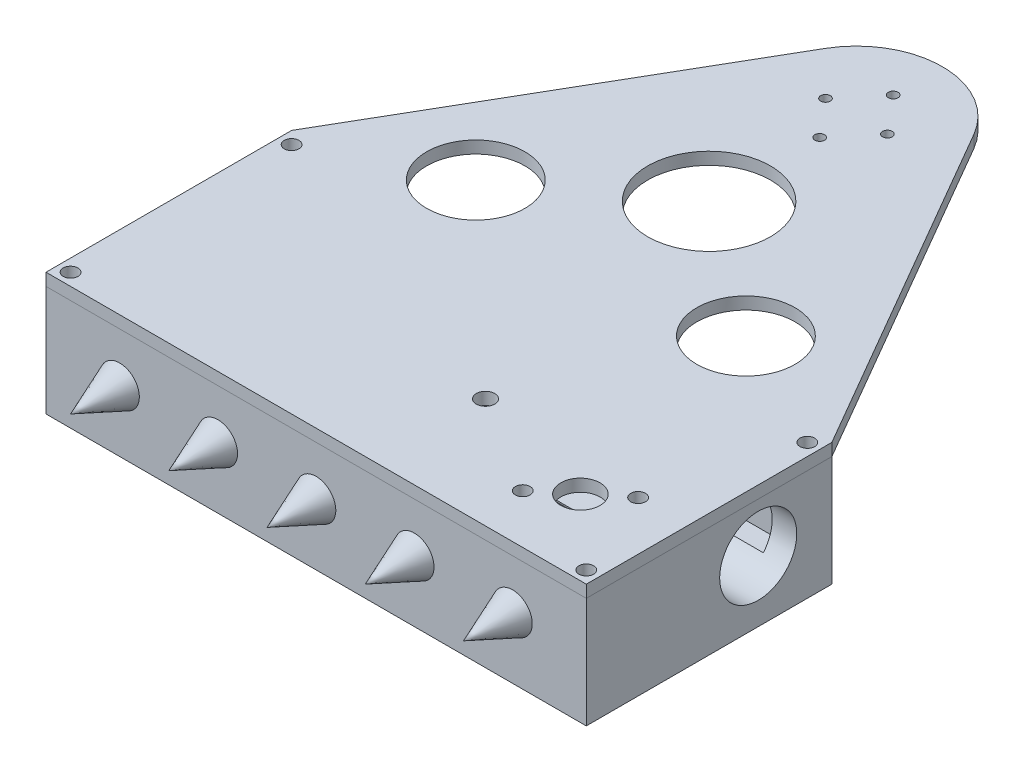
SolidWorks part; units mm, degrees
material "PLA/ABS"
ref_plane "Front Plane" through (0, 0, 0) normal (0, 0, 1) x (1, 0, 0)
ref_plane "Top Plane" through (0, 0, 0) normal (0, 1, 0) x (1, 0, 0)
ref_plane "Right Plane" through (0, 0, 0) normal (1, 0, 0) x (0, 0, -1)
other "Bounding Box"
ref_plane "Default Plane" through (-8.9266, -12.7485, 0) normal (-0.1736, 0.9848, 0) x (0.9848, 0.1736, 0)
sketch "Sketch1" plane through (0, 0, 0) normal (0, 1, 0) x (1, 0, 0)
  line L0 (0, 0) -> (0, -95.25) construction
  line L1 (0, -95.25) -> (-19.05, -95.25) construction
  line L2 (-76.2, -95.25) -> (-69.85, -95.25) construction
  line L3 (-69.85, -105.2195) -> (-19.05, -105.2195)
  line L4 (-69.85, -105.2195) -> (-69.85, -85.2805)
  line L5 (-69.85, -85.2805) -> (-19.05, -85.2805)
  line L6 (-19.05, -105.2195) -> (-19.05, -85.2805)
  line L7 (-69.85, -105.2195) -> (-19.05, -85.2805) construction
  line L8 (-69.85, -85.2805) -> (-19.05, -105.2195) construction
  line L9 (-88.9, -120.65) -> (-76.2, -120.65)
  line L10 (-88.9, -120.65) -> (-88.9, -69.85)
  line L11 (-88.9, -69.85) -> (-76.2, -69.85)
  line L12 (-76.2, -120.65) -> (-76.2, -69.85)
  line L13 (-88.9, -120.65) -> (-76.2, -69.85) construction
  line L14 (-88.9, -69.85) -> (-76.2, -120.65) construction
  line L15 (69.85, -85.2805) -> (19.05, -85.2805)
  line L16 (-63.5, -133.35) -> (-6.35, -133.35)
  line L17 (-63.5, -133.35) -> (-63.5, -116.84)
  line L18 (-63.5, -116.84) -> (-6.35, -116.84)
  line L19 (-6.35, -133.35) -> (-6.35, -116.84)
  line L20 (-63.5, -133.35) -> (-6.35, -116.84) construction
  line L21 (-63.5, -116.84) -> (-6.35, -133.35) construction
  line L22 (19.05, -105.2195) -> (19.05, -85.2805)
  line L23 (69.85, -105.2195) -> (19.05, -105.2195)
  line L24 (69.85, -105.2195) -> (69.85, -85.2805)
  line L25 (88.9, -69.85) -> (76.2, -69.85)
  line L26 (76.2, -120.65) -> (76.2, -69.85)
  line L27 (88.9, -120.65) -> (76.2, -120.65)
  line L28 (88.9, -120.65) -> (88.9, -69.85)
  line L30 (63.5, -133.35) -> (20.32, -133.35)
  line L31 (63.5, -133.35) -> (63.5, -113.2078)
  line L32 (63.5, -113.2078) -> (20.32, -113.2078)
  line L33 (20.32, -133.35) -> (20.32, -113.2078)
  line L34 (63.5, -133.35) -> (20.32, -113.2078) construction
  line L35 (63.5, -113.2078) -> (20.32, -133.35) construction
  line L36 (-69.85, -139.7) -> (69.85, -139.7)
  line L37 (-69.85, -139.7) -> (-69.85, -76.2)
  line L38 (-69.85, -76.2) -> (69.85, -76.2)
  line L39 (69.85, -139.7) -> (69.85, -76.2)
  line L40 (-69.85, -139.7) -> (69.85, -76.2) construction
  line L41 (-69.85, -76.2) -> (69.85, -139.7) construction
  circle A0 centre (0, 0) radius 69.85
  circle A1 centre (0, 0) radius 13.843
  point P3 (-34.925, -125.095)
  point P6 (-44.45, -95.25)
  point P12 (-82.55, -95.25)
  point P22 (0, -76.2)
  point P23 (0, -107.95)
  point P36 (0, -69.85)
  point P38 (41.91, -123.2789)
  dimension "D1" = 139.7
  dimension "D19" = 27.686
  dimension "D2" = 50.8
  dimension "D3" = 19.939
  dimension "D4" = 50.8
  dimension "D5" = 12.7
  dimension "D6" = 57.15
  dimension "D7" = 16.51
  dimension "D8" = 43.18
  dimension "D9" = 20.1422
  dimension "D10" = 6.35
  dimension "D11" = 139.7
  dimension "D12" = 44.45
  dimension "D13" = 6.35
  dimension "D14" = 6.35
  dimension "D15" = 6.35
  dimension "D16" = 6.35
  dimension "D17" = 63.5
  dimension "D18" = 6.35
sketch "Sketch2" plane through (0, 0, 0) normal (1, 0, 0) x (0, 0, -1)
  line L1 (-139.7, 12.7) -> (-76.2, 12.7)
  line L2 (-139.7, 12.7) -> (-139.7, -12.7)
  line L3 (-139.7, -12.7) -> (-76.2, -12.7)
  line L4 (-76.2, 12.7) -> (-76.2, -12.7)
  line L5 (-139.7, 12.7) -> (-76.2, -12.7) construction
  line L6 (-139.7, -12.7) -> (-76.2, 12.7) construction
  line L7 (-139.7, 12.7) -> (12.7, 12.7)
  line L8 (-139.7, 12.7) -> (-139.7, 15.875)
  line L9 (-139.7, 15.875) -> (12.7, 15.875)
  line L10 (12.7, 12.7) -> (12.7, 15.875)
  line L11 (-139.7, 12.7) -> (12.7, 15.875) construction
  line L12 (-139.7, 15.875) -> (12.7, 12.7) construction
  line L13 (-139.7, -12.7) -> (-76.2, -12.7)
  line L14 (-139.7, -12.7) -> (-139.7, -15.875)
  line L15 (-139.7, -15.875) -> (-76.2, -15.875)
  line L16 (-76.2, -12.7) -> (-76.2, -15.875)
  line L17 (-139.7, -12.7) -> (-76.2, -15.875) construction
  line L18 (-139.7, -15.875) -> (-76.2, -12.7) construction
  circle A0 centre (-95.25, 0) radius 25.4
  point P4 (-120.65, 0)
  point P5 (-107.95, 0)
  point P15 (-63.5, 14.2875)
  point P19 (-107.95, -14.2875)
  dimension "D1" = 25.4
  dimension "D2" = 3.175
  dimension "D3" = 12.7
sketch "Sketch3" plane through (0, 0, 0) normal (0, 1, 0) x (1, 0, 0)
  line L1 (-69.85, -139.7) -> (69.85, -139.7)
  line L2 (-69.85, -139.7) -> (-69.85, -76.2)
  line L3 (-69.85, -76.2) -> (69.85, -76.2)
  line L4 (69.85, -139.7) -> (69.85, -76.2)
  line L5 (-69.85, -139.7) -> (69.85, -76.2) construction
  line L6 (-69.85, -76.2) -> (69.85, -139.7) construction
  line L7 (-63.5, -82.55) -> (63.5, -82.55)
  line L8 (-63.5, -82.55) -> (-63.5, -133.35)
  line L9 (-63.5, -133.35) -> (63.5, -133.35)
  line L10 (63.5, -82.55) -> (63.5, -133.35)
  line L11 (-63.5, -82.55) -> (63.5, -133.35) construction
  line L12 (-63.5, -133.35) -> (63.5, -82.55) construction
  point P0 (0, -107.95)
  point P7 (0, -107.95)
extrude "Boss-Extrude1" add sketch "Sketch3" along normal up to vertex (12.7 mm away) and the other way up to vertex (12.7 mm away) up to point (0, 12.7, 139.7) other way up to point (0, -12.7, 139.7)
sketch "Sketch4" plane through (0, -12.7, 0) normal (0, -1, 0) x (1, 0, 0)
  line L1 (-69.85, 139.7) -> (69.85, 139.7)
  line L2 (-69.85, 139.7) -> (-69.85, 76.2)
  line L3 (-69.85, 76.2) -> (69.85, 76.2)
  line L4 (69.85, 139.7) -> (69.85, 76.2)
  line L5 (-69.85, 139.7) -> (69.85, 76.2) construction
  line L6 (-69.85, 76.2) -> (69.85, 139.7) construction
  point P0 (0, 107.95)
extrude "Boss-Extrude2" add sketch "Sketch4" along normal up to vertex (3.175 mm away) up to point (0, -15.875, 139.7)
sketch "Sketch5" plane through (0, 12.7, 0) normal (0, 1, 0) x (1, 0, 0)
  line L0 (-19.229, 11.1443) -> (-69.85, -76.2)
  line L1 (-69.85, -76.2) -> (-69.85, -139.7)
  line L2 (-69.85, -139.7) -> (69.85, -139.7)
  line L3 (69.85, -139.7) -> (69.85, -76.2)
  line L4 (69.85, -76.2) -> (19.229, 11.1443)
  arc A0 (-19.229, 11.1443) -> (19.229, 11.1443) centre (0, 0) cw
  dimension "D1" = 22.225
extrude "Boss-Extrude3" add sketch "Sketch5" along normal up to vertex (3.175 mm away) separate body up to point (0, 15.875, 139.7)
sketch "Sketch7" plane through (0, -12.7, 0) normal (0, 1, 0) x (1, 0, 0)
  line L0 (-19.05, -105.2195) -> (-19.05, -85.2805) construction
  line L1 (-63.5, -82.55) -> (-19.05, -82.55)
  line L2 (-63.5, -82.55) -> (-63.5, -107.95)
  line L3 (-63.5, -107.95) -> (-19.05, -107.95)
  line L4 (-19.05, -82.55) -> (-19.05, -107.95)
  line L5 (-63.5, -82.55) -> (-19.05, -107.95) construction
  line L6 (-63.5, -107.95) -> (-19.05, -82.55) construction
  line L7 (63.5, -82.55) -> (19.05, -82.55)
  line L8 (63.5, -82.55) -> (63.5, -107.95)
  line L9 (63.5, -107.95) -> (19.05, -107.95)
  line L10 (19.05, -82.55) -> (19.05, -107.95)
  line L11 (63.5, -82.55) -> (19.05, -107.95) construction
  line L12 (63.5, -107.95) -> (19.05, -82.55) construction
  line L13 (19.05, -105.2195) -> (19.05, -85.2805) construction
  line L14 (0, -95.25) -> (-19.05, -95.25) construction
  point P4 (-41.275, -95.25)
  point P10 (41.275, -95.25)
extrude "Boss-Extrude4" add sketch "Sketch7" along normal blind 6.35
sketch "Sketch6" plane through (-69.85, 0, 0) normal (-1, 0, 0) x (0, 0, 1)
  circle A0 centre (95.25, 0) radius 9.9695
extrude "Cut-Extrude1" cut sketch "Sketch6" against normal through all
ref_plane "Plane1" through (0, 0, 0) normal (1, 0, 0) x (0, 0, -1)
sketch "Sketch9" plane through (0, 0, 0) normal (1, 0, 0) x (0, 0, -1)
  line L0 (-139.7, 0) -> (-139.7, 5.08)
  line L1 (-139.7, 12.7) -> (-139.7, -15.875) construction
  line L2 (-139.7, 5.08) -> (-152.4, 0)
  line L3 (-152.4, 0) -> (-139.7, 0)
  dimension "D1" = 12.7
  dimension "D2" = 5.08
revolve "Revolve1" add sketch "Sketch9" angle 360 about L3
pattern_linear "LPattern1" count 3 spacing 25.4 along (-1, 0, 0) count 3 spacing 25.4 along (1, 0, 0) of "Revolve1"
sketch "Sketch13" plane through (0, -12.7, 0) normal (0, 1, 0) x (1, 0, 0)
  line L0 (-63.5, -107.95) -> (-19.05, -107.95) construction
  line L1 (-19.05, -82.55) -> (-48.26, -82.55)
  line L2 (-19.05, -82.55) -> (-19.05, -107.95)
  line L3 (-19.05, -107.95) -> (-48.26, -107.95)
  line L4 (-48.26, -82.55) -> (-48.26, -107.95)
  line L5 (-19.05, -82.55) -> (-48.26, -107.95) construction
  line L6 (-19.05, -107.95) -> (-48.26, -82.55) construction
  line L7 (-63.5, -82.55) -> (-63.5, -87.5644) construction
  line L9 (0, -17.4625) -> (0, 17.4625) construction
  line L10 (48.26, -82.55) -> (48.26, -107.95)
  line L11 (19.05, -107.95) -> (48.26, -107.95)
  line L12 (19.05, -82.55) -> (19.05, -107.95)
  line L13 (19.05, -82.55) -> (48.26, -82.55)
  point P4 (-33.655, -95.25)
  dimension "D1" = 15.24
extrude "Boss-Extrude5" add sketch "Sketch13" along normal blind 4.064
sketch "Sketch14" plane through (0, 0, 107.95) normal (0, 0, 1) x (1, 0, 0)
  line L0 (-48.26, -8.0762) -> (-48.26, -11.2291) construction
  line L1 (-43.18, -9.144) -> (-36.83, -9.144)
  line L2 (-43.18, -9.144) -> (-43.18, -11.684)
  line L3 (-43.18, -11.684) -> (-36.83, -11.684)
  line L4 (-36.83, -9.144) -> (-36.83, -11.684)
  line L5 (-43.18, -9.144) -> (-36.83, -11.684) construction
  line L6 (-43.18, -11.684) -> (-36.83, -9.144) construction
  line L7 (-48.26, -8.636) -> (-48.26, -9.9695) construction
  line L8 (-19.05, -6.35) -> (-63.5, -6.35) construction
  line L9 (-43.18, -5.08) -> (-36.83, -5.08)
  line L10 (-43.18, -5.08) -> (-43.18, -2.54)
  line L11 (-43.18, -2.54) -> (-36.83, -2.54)
  line L12 (-36.83, -5.08) -> (-36.83, -2.54)
  line L13 (-43.18, -5.08) -> (-36.83, -2.54) construction
  line L14 (-43.18, -2.54) -> (-36.83, -5.08) construction
  line L15 (-63.5, -12.7) -> (-19.05, -12.7) construction
  line L16 (0, -17.4625) -> (0, 17.4625) construction
  line L17 (43.18, -11.684) -> (36.83, -11.684)
  line L18 (36.83, -9.144) -> (36.83, -11.684)
  line L19 (43.18, -9.144) -> (36.83, -9.144)
  line L20 (43.18, -9.144) -> (43.18, -11.684)
  line L21 (43.18, -2.54) -> (36.83, -2.54)
  line L22 (36.83, -5.08) -> (36.83, -2.54)
  line L23 (43.18, -5.08) -> (36.83, -5.08)
  line L24 (43.18, -5.08) -> (43.18, -2.54)
  point P4 (-40.005, -10.414)
  point P13 (-40.005, -3.81)
  dimension "D1" = 2.54
  dimension "D2" = 6.35
  dimension "D3" = 5.08
  dimension "D4" = 1.27
  dimension "D5" = 1.016
extrude "Cut-Extrude2" cut sketch "Sketch14" against normal up to surface (31.75 mm away) up to face at (0, -1.5875, 76.2)
sketch "Sketch18" plane through (0, 0, 82.55) normal (0, 0, 1) x (1, 0, 0)
  line L0 (63.5, 12.7) -> (-63.5, 12.7) construction
  line L1 (-60.96, 12.7) -> (-50.8, 12.7)
  line L2 (-60.96, 12.7) -> (-60.96, 7.62)
  line L3 (-60.96, 7.62) -> (-50.8, 7.62)
  line L4 (-50.8, 12.7) -> (-50.8, 7.62)
  line L5 (-60.96, 12.7) -> (-50.8, 7.62) construction
  line L6 (-60.96, 7.62) -> (-50.8, 12.7) construction
  line L7 (-63.5, 12.7) -> (-63.5, -6.35) construction
  point P4 (-55.88, 10.16)
  dimension "D1" = 10.16
  dimension "D2" = 2.54
  dimension "D3" = 5.08
extrude "Cut-Extrude3" cut sketch "Sketch18" against normal up to surface (6.35 mm away) up to face at (-40.005, -3.81, 76.2)
sketch "Sketch19" plane through (0, 12.7, 0) normal (0, 1, 0) x (1, 0, 0)
  line L0 (-69.85, -76.2) -> (-69.85, -139.7) construction
  line L1 (-60.96, -76.2) -> (-69.85, -76.2) construction
  line L2 (-63.5, -82.55) -> (-63.5, -133.35) construction
  line L5 (69.85, -139.7) -> (69.85, -76.2) construction
  line L6 (69.85, -76.2) -> (-50.8, -76.2) construction
  line L7 (-69.85, -139.7) -> (69.85, -139.7) construction
  line L8 (-63.5, -133.35) -> (63.5, -133.35) construction
  circle A0 centre (-66.675, -79.375) radius 3.175 construction
  circle A1 centre (-66.675, -79.375) radius 0.635
  circle A2 centre (66.675, -79.375) radius 3.175 construction
  circle A3 centre (66.675, -79.375) radius 0.635
  circle A4 centre (-66.675, -136.525) radius 3.175 construction
  circle A5 centre (-66.675, -136.525) radius 0.635
  circle A6 centre (66.675, -136.525) radius 3.175 construction
  circle A7 centre (66.675, -136.525) radius 0.635
  dimension "D1" = 1.27
  dimension "D2" = 6.35
extrude "Cut-Extrude4" cut sketch "Sketch19" against normal blind 25.4
sketch "Sketch20" plane through (0, 15.875, 0) normal (0, 1, 0) x (1, 0, 0)
  circle A0 centre (-66.675, -79.375) radius 1.905
  circle A1 centre (-66.675, -136.525) radius 1.905
  circle A2 centre (66.675, -136.525) radius 1.905
  circle A3 centre (66.675, -79.375) radius 1.905
  dimension "D1" = 3.81
  dimension "D2" = 3.81
  dimension "D3" = 3.81
  dimension "D4" = 3.81
extrude "Cut-Extrude7" cut sketch "Sketch20" against normal up to surface (3.175 mm away) up to face at (0, 12.7, 66.4051)
sketch "Sketch23" plane through (0, 15.875, 0) normal (0, 1, 0) x (1, 0, 0)
  line L0 (-69.85, -139.7) -> (69.85, -139.7) construction
  line L1 (57.15, -113.6085) -> (40.715, -113.6085) construction
  line L2 (57.15, -113.6085) -> (57.15, -127) construction
  line L3 (57.15, -127) -> (40.715, -127) construction
  line L4 (40.715, -113.6085) -> (40.715, -127) construction
  line L5 (57.15, -113.6085) -> (40.715, -127) construction
  line L6 (57.15, -127) -> (40.715, -113.6085) construction
  line L7 (69.85, -139.7) -> (69.85, -76.2) construction
  circle A0 centre (48.9325, -120.3043) radius 5.08
  circle A1 centre (57.15, -113.6085) radius 1.905
  circle A2 centre (40.715, -127) radius 1.905
  circle A4 centre (15.315, -111.2273) radius 2.3812
  point P0 (48.9325, -120.3043)
  dimension "D1" = 10.16
  dimension "D2" = 3.81
  dimension "D3" = 10.6
  dimension "D4" = 12.7
  dimension "D7" = 4.7625
  dimension "D8" = 25.4
  dimension "D5" = 12.7
  dimension "D6" = 13.3915
extrude "Cut-Extrude8" cut sketch "Sketch23" against normal up to surface (3.175 mm away) up to face at (-66.675, 12.7, 77.47)
sketch "Sketch24" plane through (0, 15.875, 0) normal (0, 1, 0) x (1, 0, 0)
  circle A0 centre (0, 0) radius 8 construction
  circle A1 centre (0, 0) radius 9.5 construction
  circle A2 centre (0, 9.5) radius 1.25
  circle A3 centre (0, -9.5) radius 1.25
  circle A4 centre (-8, 0) radius 1.25
  circle A5 centre (8, 0) radius 1.25
  dimension "D1" = 19
  dimension "D2" = 16
  dimension "D3" = 2.5
  dimension "D4" = 2.5
  dimension "D5" = 2.5
  dimension "D6" = 2.5
extrude "Cut-Extrude9" cut sketch "Sketch24" against normal up to surface (3.175 mm away) up to face at (15.315, 12.7, 108.846)
sketch "Sketch25" plane through (0, 15.875, 0) normal (0, 1, 0) x (1, 0, 0)
  line L0 (-34.925, -63.5) -> (0, -38.1) construction
  line L1 (0, -38.1) -> (34.925, -63.5) construction
  line L2 (34.925, -63.5) -> (-34.925, -63.5) construction
  line L3 (0, -63.5) -> (0, 0) construction
  line L4 (-69.85, -76.2) -> (69.85, -76.2) construction
  circle A0 centre (0, -38.1) radius 15.875
  circle A1 centre (-34.925, -63.5) radius 12.7
  circle A2 centre (34.925, -63.5) radius 12.7
  arc A3 (19.229, 11.1443) -> (-19.229, 11.1443) centre (0, 0) ccw construction
  dimension "D1" = 31.75
  dimension "D2" = 25.4
  dimension "D3" = 69.85
extrude "Cut-Extrude10" cut sketch "Sketch25" against normal through all
delete or keep bodies "Body-Delete/Keep 1" [suppressed] type delete bodies bodies 114
